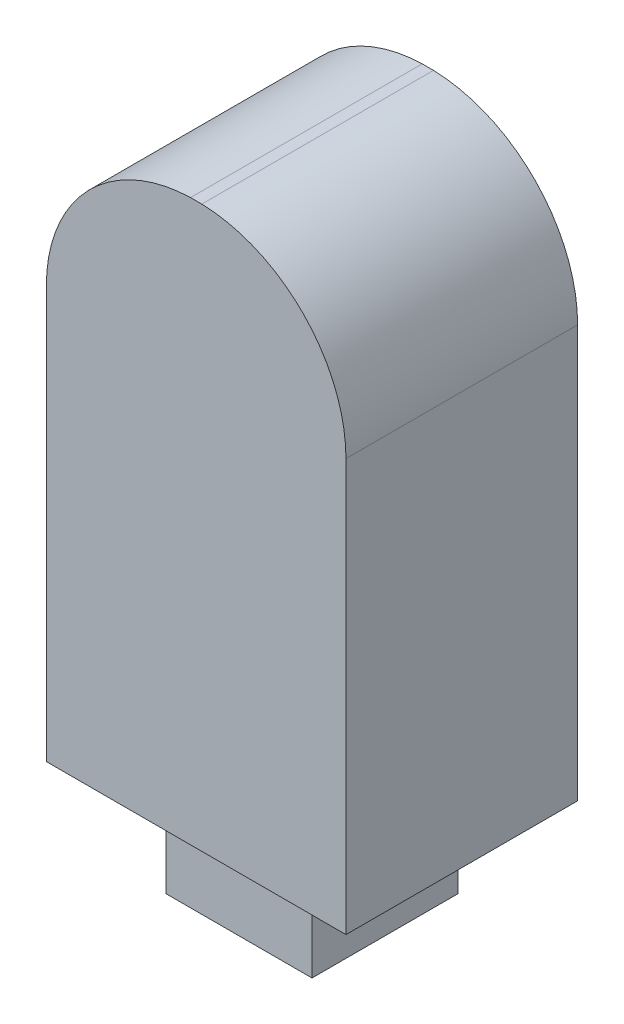
SolidWorks part; units mm, degrees
ref_plane "Front Plane" through (0, 0, 0) normal (0, 0, 1) x (1, 0, 0)
ref_plane "Top Plane" through (0, 0, 0) normal (0, 1, 0) x (1, 0, 0)
ref_plane "Right Plane" through (0, 0, 0) normal (1, 0, 0) x (0, 0, -1)
sketch "Sketch1" plane through (0, 0, 0) normal (0, 0, 1) x (1, 0, 0)
  line L0 (0, 0) -> (0, -12.7)
  line L1 (0, -12.7) -> (9.2304, -12.7)
  line L2 (9.2304, -12.7) -> (9.2304, 0)
  line L3 (4.4415, 4.5701) -> (4.7889, 4.5701)
  arc A1 (0, 0) -> (4.4415, 4.5701) centre (4.572, 0) cw
  arc A2 (9.2304, 0) -> (4.7889, 4.5701) centre (4.6584, 0) ccw
  point P9 (4.6152, 4.5701)
  point P10 (4.6152, -12.7)
  point P11 (4.5232, 5.4064)
  point P12 (4.7518, 4.571)
  point P13 (5.0974, 4.5509)
  point P14 (4.7889, 4.5701)
  dimension "D4" = 4.572
  dimension "D5" = 4.572
  dimension "D1" = 9.2304
  dimension "D2" = 12.7
  dimension "D3" = 12.7
extrude "Boss-Extrude1" add sketch "Sketch1" along normal blind 7.1374
sketch "Sketch2" plane through (0, -12.7, 0) normal (0, -1, 0) x (1, 0, 0)
  line L0 (0, 0) -> (9.2304, 7.1374) construction
  line L2 (6.8652, 1.3187) -> (2.3652, 1.3187)
  line L3 (6.8652, 1.3187) -> (6.8652, 5.8187)
  line L4 (6.8652, 5.8187) -> (2.3652, 5.8187)
  line L5 (2.3652, 1.3187) -> (2.3652, 5.8187)
  line L6 (6.8652, 1.3187) -> (2.3652, 5.8187) construction
  line L7 (6.8652, 5.8187) -> (2.3652, 1.3187) construction
  point P4 (4.6152, 3.5687)
  dimension "D1" = 4.5
  dimension "D2" = 4.5
extrude "Boss-Extrude2" add sketch "Sketch2" along normal blind 3
